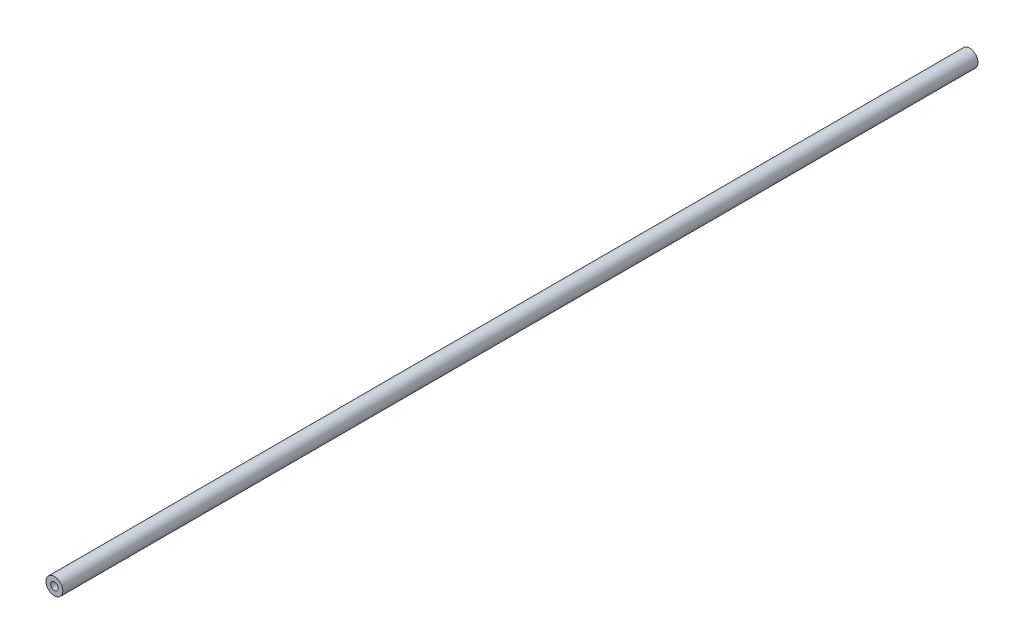
SolidWorks part; units mm, degrees
material "AISI 1045 钢，冷拔"
ref_plane "前视基准面" through (0, 0, 0) normal (0, 0, 1) x (1, 0, 0)
ref_plane "上视基准面" through (0, 0, 0) normal (0, 1, 0) x (1, 0, 0)
ref_plane "右视基准面" through (0, 0, 0) normal (1, 0, 0) x (0, 0, -1)
sketch "草图1" plane through (0, 0, 0) normal (0, 0, 1) x (1, 0, 0)
  circle A0 centre (0, 0) radius 4.5
  circle A1 centre (0, 0) radius 2
extrude "凸台-拉伸1" add sketch "草图1" along normal blind 490
